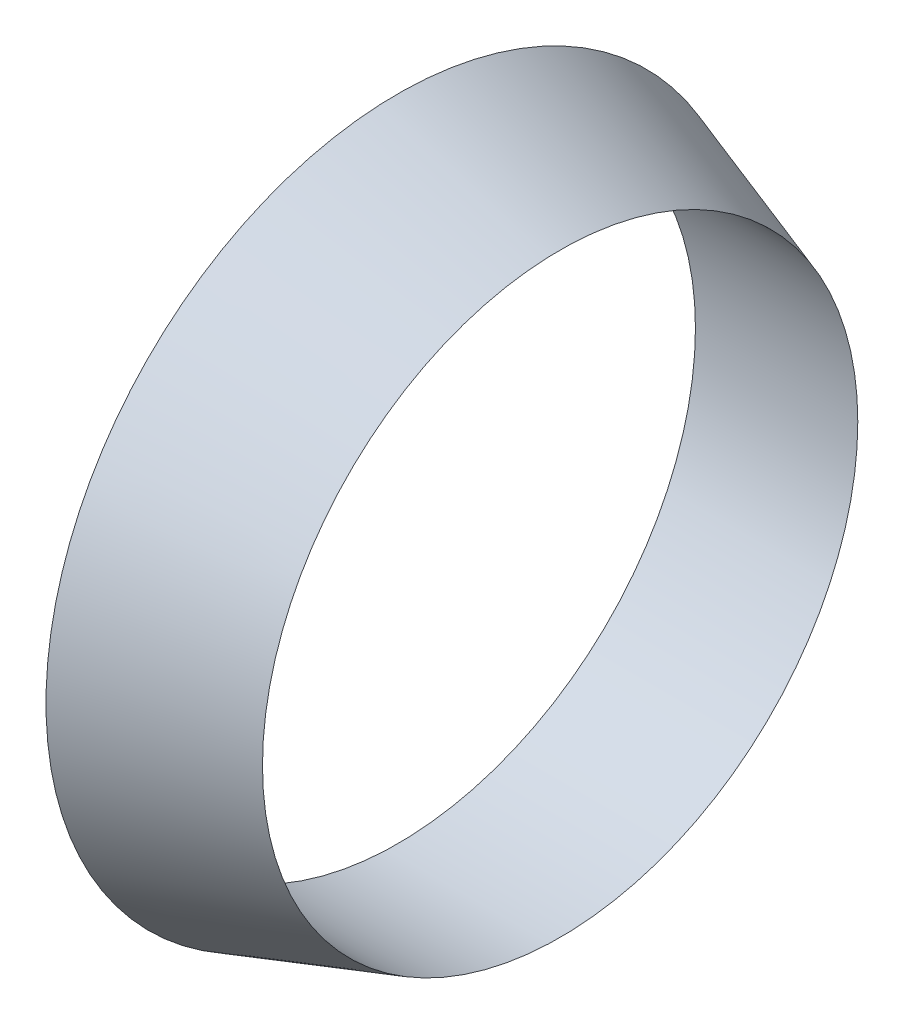
SolidWorks part; units mm, degrees
ref_plane "Front Plane" through (0, 0, 0) normal (0, 0, 1) x (1, 0, 0)
ref_plane "Top Plane" through (0, 0, 0) normal (0, 1, 0) x (1, 0, 0)
ref_plane "Right Plane" through (0, 0, 0) normal (1, 0, 0) x (0, 0, -1)
sketch "Sketch1" plane through (0, 0, 0) normal (1, 0, 0) x (0, 0, -1)
  circle A0 centre (0, 0) radius 65
  dimension "D1" = 130
ref_plane "Plane1" through (30, 0, 0) normal (1, 0, 0) x (0, 0, -1)
sketch "Sketch2" plane through (30, 0, 0) normal (1, 0, 0) x (0, 0, -1)
  circle A0 centre (0, 0) radius 55
  dimension "D1" = 110
loft "Loft1" add profiles "Sketch1", "Sketch2"
sketch "Sketch3" plane through (30, 0, 0) normal (1, 0, 0) x (0, 0, -1)
  circle A1 centre (0, 0) radius 55
  circle A2 centre (0, 0) radius 55
  dimension "D1" = 0
extrude "Cut-Extrude1" cut sketch "Sketch3" against normal through all
